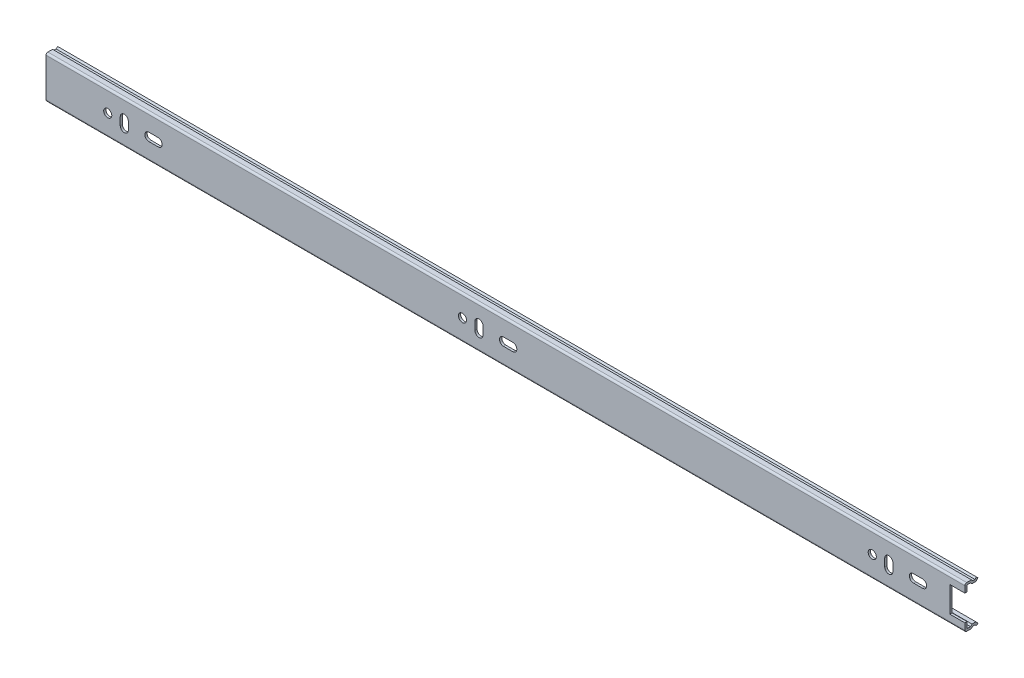
SolidWorks part; units mm, degrees
ref_plane "Спереди" through (0, 0, 0) normal (0, 0, 1) x (1, 0, 0)
ref_plane "Сверху" through (0, 0, 0) normal (0, 1, 0) x (1, 0, 0)
ref_plane "Справа" through (0, 0, 0) normal (1, 0, 0) x (0, 0, -1)
sketch "Эскиз1" plane through (0, 0, 0) normal (1, 0, 0) x (0, 0, -1)
  line L0 (0, 10.5) -> (0, -10.5)
  line L1 (-12.4481, 0) -> (26.4522, 0) construction
  line L2 (3.5733, 11.5) -> (1, 11.5)
  line L3 (4.3714, 10.7019) -> (3.5733, 11.5)
  line L4 (5.5019, 10.7019) -> (4.3714, 10.7019)
  line L5 (6.3, -11.5) -> (5.5019, -10.7019)
  line L6 (5.5019, -10.7019) -> (4.3714, -10.7019)
  line L7 (4.3714, -10.7019) -> (3.5733, -11.5)
  line L8 (3.5733, -11.5) -> (1, -11.5)
  line L9 (6.3, 11.5) -> (5.5019, 10.7019)
  arc A0 (0, 10.5) -> (1, 11.5) centre (1, 10.5) cw
  arc A2 (0, -10.5) -> (1, -11.5) centre (1, -10.5) ccw
  point P0 (0, -11.5)
  point P1 (0, 11.5)
  point P12 (0, 0)
  point P20 (0, 0)
extrude "Вытянуть-Тонкостенный3" add sketch "Эскиз1" along normal blind 500 thin
sketch "Эскиз2" plane through (0, 0, 0) normal (0, 0, 1) x (1, 0, 0)
  line L0 (500, -10.5) -> (500, 10.5) construction
  line L1 (500, 7) -> (491.8, 7)
  line L2 (500, 7) -> (500, -7)
  line L3 (500, -7) -> (491.8, -7)
  line L4 (491.8, 7) -> (491.8, -7)
  line L5 (472, 2.2) -> (477, 2.2)
  line L6 (472, -2.2) -> (477, -2.2)
  line L7 (456.4, 1.7796) -> (456.4, -2.5)
  line L8 (460.8, -2.5) -> (460.8, 1.7796)
  line L9 (233.4, 1.7796) -> (233.4, -2.5)
  line L10 (237.8, -2.5) -> (237.8, 1.7796)
  line L11 (249, -2.2) -> (254, -2.2)
  line L12 (249, 2.2) -> (254, 2.2)
  line L13 (44.8, -2.5) -> (44.8, 1.7796)
  line L14 (40.4, 1.7796) -> (40.4, -2.5)
  line L15 (56, 2.2) -> (61, 2.2)
  line L16 (56, -2.2) -> (61, -2.2)
  circle A0 centre (449.6, 0) radius 2.2
  arc A1 (472, 2.2) -> (472, -2.2) centre (472, 0) ccw
  arc A2 (477, 2.2) -> (477, -2.2) centre (477, 0) cw
  arc A3 (456.4, -2.5) -> (460.8, -2.5) centre (458.6, -2.5) ccw
  arc A4 (460.8, 1.7796) -> (456.4, 1.7796) centre (458.6, 1.7796) ccw
  arc A5 (233.4, -2.5) -> (237.8, -2.5) centre (235.6, -2.5) ccw
  circle A6 centre (226.6, 0) radius 2.2
  arc A7 (237.8, 1.7796) -> (233.4, 1.7796) centre (235.6, 1.7796) ccw
  arc A8 (249, 2.2) -> (249, -2.2) centre (249, 0) ccw
  arc A9 (254, 2.2) -> (254, -2.2) centre (254, 0) cw
  arc A10 (40.4, -2.5) -> (44.8, -2.5) centre (42.6, -2.5) ccw
  arc A11 (44.8, 1.7796) -> (40.4, 1.7796) centre (42.6, 1.7796) ccw
  circle A12 centre (33.6, 0) radius 2.2
  arc A13 (61, 2.2) -> (61, -2.2) centre (61, 0) cw
  arc A14 (56, 2.2) -> (56, -2.2) centre (56, 0) ccw
extrude "Вырез-Вытянуть1" cut sketch "Эскиз2" against normal through all
